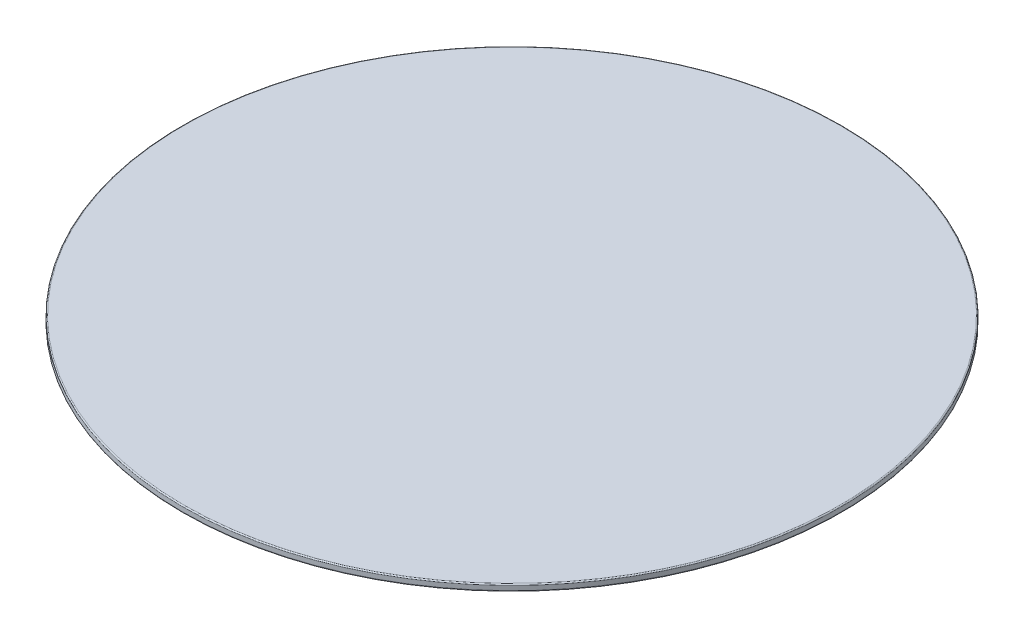
SolidWorks part; units mm, degrees
material "Glass"
ref_plane "Front Plane" through (0, 0, 0) normal (0, 0, 1) x (1, 0, 0)
ref_plane "Top Plane" through (0, 0, 0) normal (0, 1, 0) x (1, 0, 0)
ref_plane "Right Plane" through (0, 0, 0) normal (1, 0, 0) x (0, 0, -1)
sketch "Sketch1" plane through (0, 0, 0) normal (0, 1, 0) x (1, 0, 0)
  circle A0 centre (0, 0) radius 150
  dimension "D1" = 300
extrude "Boss-Extrude1" add sketch "Sketch1" along normal blind 3
fillet "Fillet1" radius 0.5 2 edges at (0, 3, 150) (0, 0, 150)
